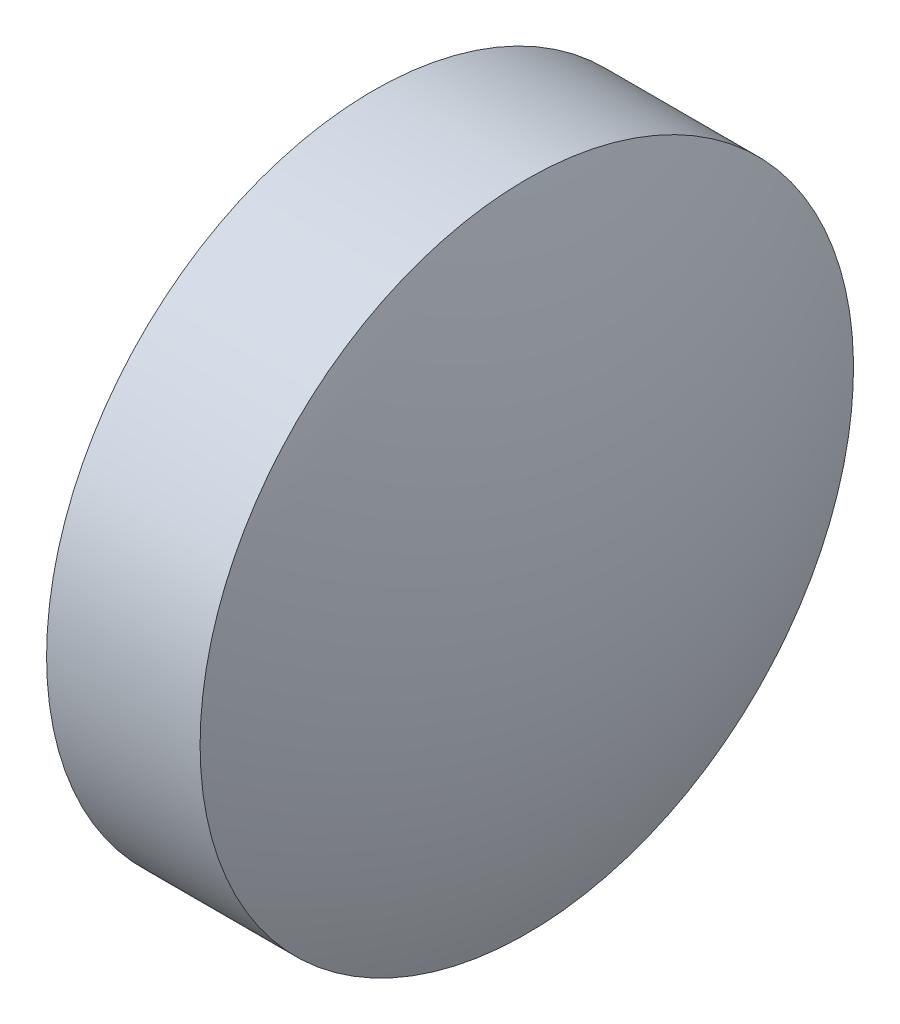
SolidWorks part; units mm, degrees
ref_plane "前视基准面" through (0, 0, 0) normal (0, 0, 1) x (1, 0, 0)
ref_plane "上视基准面" through (0, 0, 0) normal (0, 1, 0) x (1, 0, 0)
ref_plane "右视基准面" through (0, 0, 0) normal (1, 0, 0) x (0, 0, -1)
sketch "草图1" plane through (0, 0, 0) normal (0, 0, 1) x (1, 0, 0)
  line L0 (442.2177, -98.4397) -> (447.6127, -98.4397) construction
  line L1 (443.0234, -98.4397) -> (443.0234, -95.2897)
  line L2 (445.1234, -98.4397) -> (443.0234, -98.4397)
  line L5 (443.0234, -95.2897) -> (444.5034, -95.2897)
  arc A0 (445.1234, -98.4397) -> (444.5034, -95.2897) centre (436.8114, -98.4397) ccw
revolve "旋转1" add sketch "草图1" angle 360 about L0
